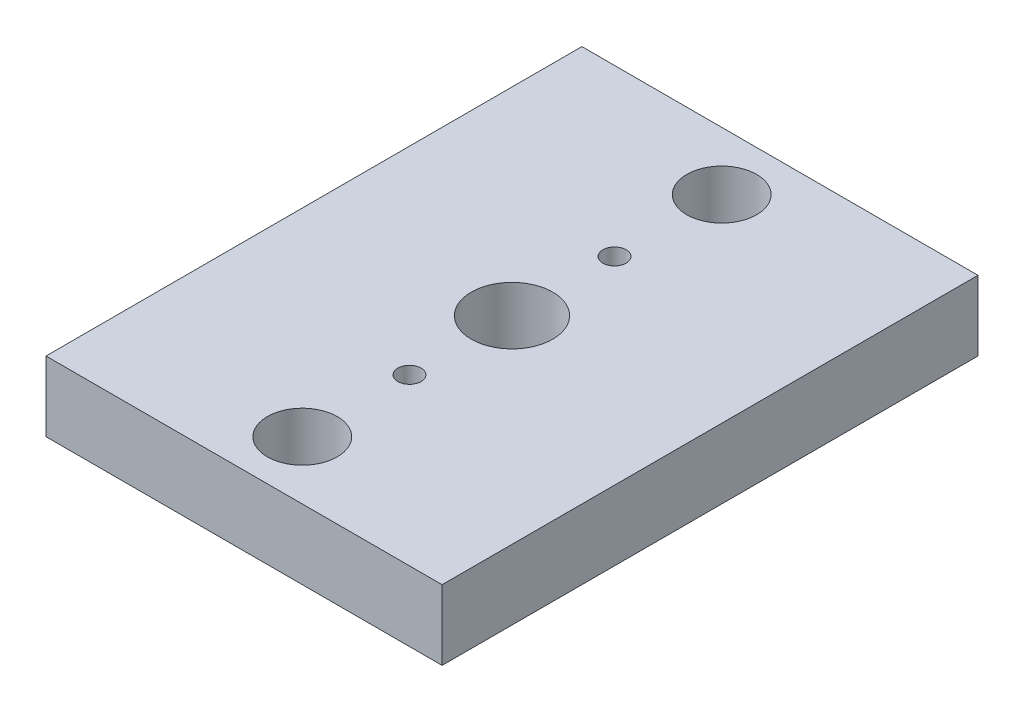
SolidWorks part; units mm, degrees
ref_plane "Front Plane" through (0, 0, 0) normal (0, 0, 1) x (1, 0, 0)
ref_plane "Top Plane" through (0, 0, 0) normal (0, 1, 0) x (1, 0, 0)
ref_plane "Right Plane" through (0, 0, 0) normal (1, 0, 0) x (0, 0, -1)
sketch "Sketch1" plane through (0, 0, 0) normal (0, 1, 0) x (1, 0, 0)
  line L1 (8.5, -11.5) -> (-8.5, -11.5)
  line L2 (8.5, -11.5) -> (8.5, 11.5)
  line L3 (8.5, 11.5) -> (-8.5, 11.5)
  line L4 (-8.5, -11.5) -> (-8.5, 11.5)
  line L5 (8.5, -11.5) -> (-8.5, 11.5) construction
  line L6 (8.5, 11.5) -> (-8.5, -11.5) construction
  point P0 (0, 0)
  dimension "D1" = 17
  dimension "D2" = 23
extrude "Boss-Extrude1" add sketch "Sketch1" along normal blind 3
sketch "Sketch2" plane through (0, 3, 0) normal (0, 1, 0) x (1, 0, 0)
  line L0 (0, 11.5) -> (0, -11.5) construction
  line L1 (8.5, 11.5) -> (-8.5, 11.5) construction
  line L2 (-8.5, -11.5) -> (8.5, -11.5) construction
  line L3 (-8.5, 0) -> (8.5, 0) construction
  line L4 (-8.5, 11.5) -> (-8.5, -11.5) construction
  line L5 (8.5, -11.5) -> (8.5, 11.5) construction
  line L6 (-8.5, 5.9) -> (8.5, 5.9) construction
  line L7 (-8.5, -5.9) -> (8.5, -5.9) construction
  circle A0 centre (0, 9) radius 1.5
  circle A2 centre (0, 4.4) radius 0.5
  circle A3 centre (0, -4.4) radius 0.5
  circle A4 centre (0, -9) radius 1.5
  dimension "D1" = 1
  dimension "D2" = 3
  dimension "D3" = 2.5
  dimension "D4" = 5.9
  dimension "D5" = 1.5
extrude "Cut-Extrude1" cut sketch "Sketch2" against normal through all
sketch "Sketch3" plane through (0, 3, 0) normal (0, 1, 0) x (1, 0, 0)
  circle A0 centre (0, 0) radius 1.75
  dimension "D1" = 3.5
extrude "Cut-Extrude2" cut sketch "Sketch3" against normal through all
